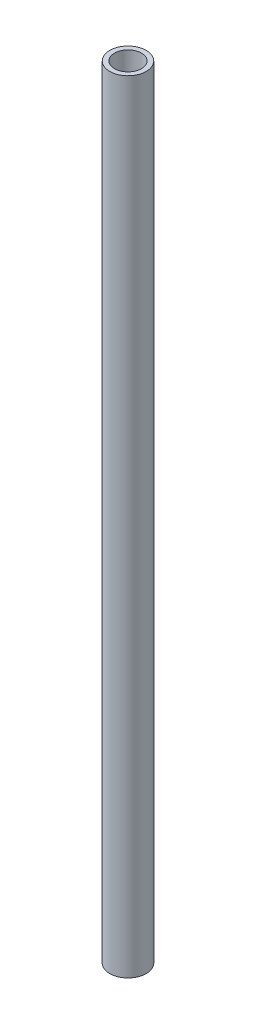
SolidWorks part; units mm, degrees
ref_plane "Front Plane" through (0, 0, 0) normal (0, 0, 1) x (1, 0, 0)
ref_plane "Top Plane" through (0, 0, 0) normal (0, 1, 0) x (1, 0, 0)
ref_plane "Right Plane" through (0, 0, 0) normal (1, 0, 0) x (0, 0, -1)
sketch "Sketch1" plane through (0, 0, 0) normal (0, 1, 0) x (1, 0, 0)
  circle A0 centre (0, 0) radius 7.8994
  circle A1 centre (0, 0) radius 10.668
  dimension "D1" = 21.336
  dimension "D2" = 15.7988
extrude "Boss-Extrude1" add sketch "Sketch1" along normal blind 457.2
